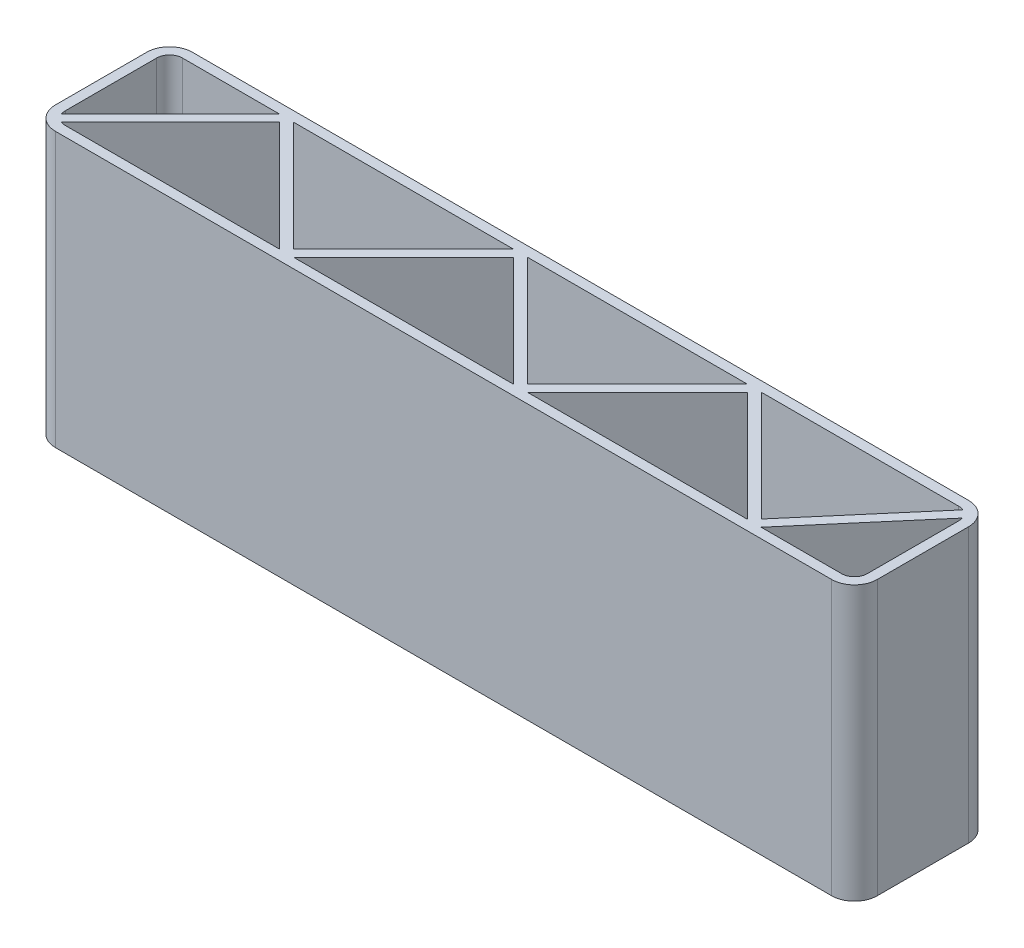
SolidWorks part; units mm, degrees
ref_plane "Front Plane" through (0, 0, 0) normal (0, 0, 1) x (1, 0, 0)
ref_plane "Top Plane" through (0, 0, 0) normal (0, 1, 0) x (1, 0, 0)
ref_plane "Right Plane" through (0, 0, 0) normal (1, 0, 0) x (0, 0, -1)
sketch "Sketch1" plane through (0, 0, 0) normal (0, 1, 0) x (1, 0, 0)
  line L1 (-863.6, 152.4) -> (863.6, 152.4)
  line L2 (-914.4, 101.6) -> (-914.4, -101.6)
  line L3 (-863.6, -152.4) -> (863.6, -152.4)
  line L4 (914.4, 101.6) -> (914.4, -101.6)
  line L5 (-914.4, 152.4) -> (914.4, -152.4) construction
  line L6 (-914.4, -152.4) -> (914.4, 152.4) construction
  arc A0 (863.6, 152.4) -> (914.4, 101.6) centre (863.6, 101.6) cw
  arc A1 (863.6, -152.4) -> (914.4, -101.6) centre (863.6, -101.6) ccw
  arc A2 (-914.4, -101.6) -> (-863.6, -152.4) centre (-863.6, -101.6) ccw
  arc A3 (-863.6, 152.4) -> (-914.4, 101.6) centre (-863.6, 101.6) ccw
  point P0 (0, 0)
  dimension "D3" = 50.8
  dimension "D1" = 1828.8
  dimension "D2" = 304.8
extrude "Extrude-Thin1" add sketch "Sketch1" along normal blind 609.6 thin
sketch "Sketch2" plane through (0, 609.6, 0) normal (0, 1, 0) x (1, 0, 0)
  line L0 (-892.175, -130.175) -> (-631.825, 130.175)
  line L1 (863.6, 130.175) -> (-863.6, 130.175) construction
  line L2 (-631.825, 130.175) -> (-371.475, -130.175)
  line L3 (-863.6, -130.175) -> (863.6, -130.175) construction
  line L4 (-371.475, -130.175) -> (-111.125, 130.175)
  line L5 (-111.125, 130.175) -> (149.225, -130.175)
  line L6 (149.225, -130.175) -> (409.575, 130.175)
  line L7 (409.575, 130.175) -> (669.925, -130.175)
  line L8 (669.925, -130.175) -> (892.175, 130.175)
  point P2 (-892.175, -130.175)
  point P7 (0, 0)
  point P16 (892.175, 130.175)
extrude "Extrude-Thin3" add sketch "Sketch2" against normal up to vertex (609.6 mm away) thin thin type mid plane wall 22.225
